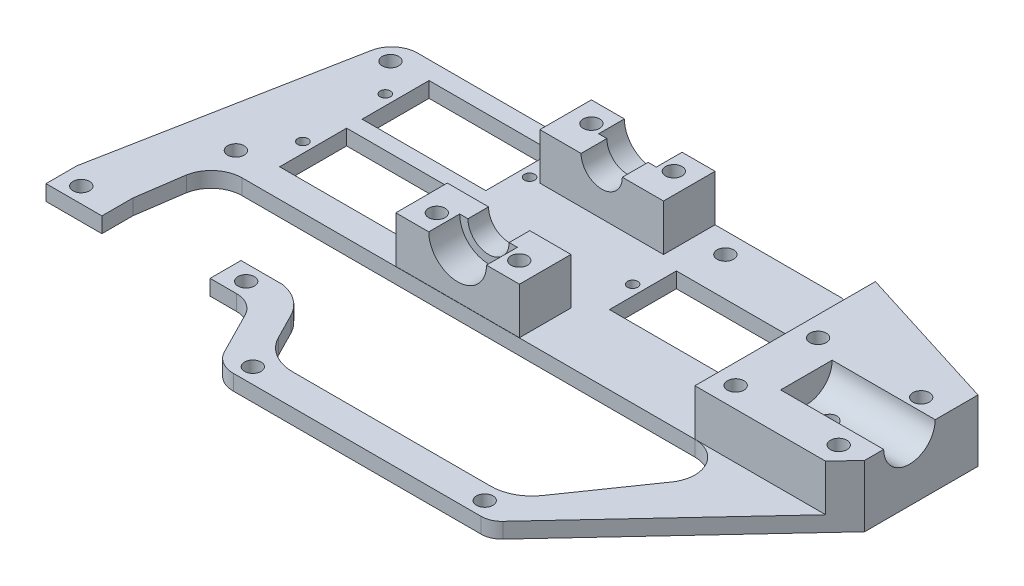
SolidWorks part; units mm, degrees
ref_plane "Спереди" through (0, 0, 0) normal (0, 0, 1) x (1, 0, 0)
ref_plane "Сверху" through (0, 0, 0) normal (0, 1, 0) x (1, 0, 0)
ref_plane "Справа" through (0, 0, 0) normal (1, 0, 0) x (0, 0, -1)
sketch "Эскиз1" plane through (0, 0, 0) normal (0, 1, 0) x (1, 0, 0)
  line L0 (0, 20) -> (0, -20) construction
  line L1 (16, 6.5) -> (40, 6.5)
  line L2 (-40, 14.5) -> (-16, 14.5)
  line L3 (-40, 14.5) -> (-40, 1.5)
  line L4 (-40, 1.5) -> (-16, 1.5)
  line L5 (-16, 14.5) -> (-16, 1.5)
  line L6 (-40, 14.5) -> (-16, 1.5) construction
  line L7 (-40, 1.5) -> (-16, 14.5) construction
  line L8 (-40, -1.5) -> (-16, -1.5)
  line L9 (-40, -1.5) -> (-40, -14.5)
  line L10 (-40, -14.5) -> (-16, -14.5)
  line L11 (-16, -1.5) -> (-16, -14.5)
  line L12 (-40, -1.5) -> (-16, -14.5) construction
  line L13 (-40, -14.5) -> (-16, -1.5) construction
  line L14 (-28, 8) -> (-28, -8) construction
  line L15 (0, 20) -> (-56.8521, 20) construction
  line L16 (0, 20) -> (59.9648, 20) construction
  line L17 (0, -20) -> (57.5525, -20) construction
  line L18 (0, -20) -> (-56.8521, -20) construction
  line L19 (16, 6.5) -> (16, -6.5)
  line L20 (16, -6.5) -> (40, -6.5)
  line L21 (40, 6.5) -> (40, -6.5)
  line L22 (16, 6.5) -> (40, -6.5) construction
  line L23 (16, -6.5) -> (40, 6.5) construction
  line L24 (28, 20) -> (28, -20) construction
  line L25 (-56.8521, 14) -> (93.1479, 14) construction
  line L26 (-56.8521, -16) -> (93.1479, -16) construction
  line L27 (-40, -37) -> (-56, -37) construction
  line L28 (-40, -37) -> (-24, -37) construction
  line L29 (-40, -14.5) -> (-40, -37) construction
  line L30 (-59.8465, -34) -> (-19.8465, -34) construction
  line L31 (-19.8465, -34) -> (-19.8465, -40) construction
  line L32 (-19.8465, -40) -> (-59.8465, -40) construction
  line L33 (-59.8465, -40) -> (-59.8465, -34) construction
  line L34 (-59.8465, -34) -> (-49.8878, 18)
  line L35 (36.6127, 18) -> (-49.8878, 18)
  line L36 (36.6127, 18) -> (75.1122, 5.9202)
  line L37 (-47.6771, -24.9007) -> (-49.0001, -34)
  line L38 (50, -16) -> (70, -16) construction
  line L39 (-59.8465, -34) -> (-59.8465, -40)
  line L40 (-59.8465, -40) -> (-19.8465, -40)
  line L41 (-19.8465, -40) -> (-14.2549, -50.9742)
  line L42 (-9.7998, -53.7042) -> (38.319, -53.7042)
  line L43 (75.1122, 5.9202) -> (75.1122, -16.0798)
  line L44 (50, 0) -> (50, -16) construction
  line L45 (-4.2859, -47.7018) -> (34.1658, -47.7018)
  line L46 (-49.0001, -34) -> (-22.2977, -34)
  line L47 (-13.9887, -38.2804) -> (-11.4139, -43.3337)
  line L48 (-41.7786, -20) -> (46.0945, -20)
  line L49 (40.7412, -44.2586) -> (51.0261, -29.4176)
  line L50 (-20.5914, -50.7042) -> (71.7063, -50.7042) construction
  line L51 (-20.5914, -53.7042) -> (73.7938, -53.7042) construction
  line L52 (0, -16) -> (0, -104.4432) construction
  line L53 (-47, 14) -> (-47, -16) construction
  line L54 (50, 0) -> (70, -16) construction
  line L55 (-44.6457, 8) -> (-11.6511, 8) construction
  line L56 (-47.6771, -8) -> (-3.6396, -8) construction
  line L57 (8, 0) -> (46.0945, 0) construction
  line L58 (50, 0) -> (70, 0) construction
  line L59 (75.1122, -16.0798) -> (41.2457, -52.4308)
  line L60 (-49.0001, -34) -> (-49.0001, -40) construction
  line L61 (-22.2977, -34) -> (-19.8465, -34)
  circle A0 centre (-8, 14) radius 1.6
  circle A1 centre (8, 14) radius 1.6
  circle A2 centre (-8, -16) radius 1.6
  circle A3 centre (8, -16) radius 1.6
  circle A4 centre (-47, 14) radius 1.6
  circle A5 centre (70, 0) radius 1.6
  circle A6 centre (50, 0) radius 1.6
  circle A7 centre (18, 14) radius 1.6
  circle A8 centre (-47, -16) radius 1.6
  circle A9 centre (-56, -37) radius 1.6
  circle A10 centre (-24, -37) radius 1.6
  circle A11 centre (50, -16) radius 1.6
  circle A12 centre (70, -16) radius 1.6
  arc A13 (-41.7786, -20) -> (-47.6771, -24.9007) centre (-41.7786, -26) ccw
  arc A14 (-19.8465, -34) -> (-13.9887, -38.2804) centre (-21.3286, -42.1767) cw
  arc A15 (-4.2859, -47.7018) -> (-11.4139, -43.3337) centre (-4.2859, -39.7018) cw
  arc A16 (40.7412, -44.2586) -> (34.1658, -47.7018) centre (34.1658, -39.7018) cw
  arc A17 (51.0261, -29.4176) -> (46.0945, -20) centre (46.0945, -26) ccw
  arc A18 (41.2457, -52.4308) -> (38.319, -53.7042) centre (38.319, -49.7042) cw
  arc A19 (-9.7998, -53.7042) -> (-14.2549, -50.9742) centre (-9.7998, -48.7042) cw
  circle A20 centre (-9, -50.7042) radius 1.6
  circle A21 centre (36, -50.7042) radius 1.6
  circle A22 centre (60, -8) radius 1.6
  circle A23 centre (-42, -8) radius 1
  circle A24 centre (-14, -8) radius 1
  circle A25 centre (-42, 8) radius 1
  circle A26 centre (-14, 8) radius 1
  circle A27 centre (14, 0) radius 1
  circle A28 centre (42, 0) radius 1
  point P2 (-28, 8)
  point P7 (0, 0)
  point P10 (28, 0)
  point P11 (-28, -8)
  point P35 (0, 14)
  point P41 (0, -16)
  point P77 (-46.7637, -20)
  point P86 (40.0593, -53.7042)
  point P92 (-49.0001, -34)
  dimension "D10" = 16
  dimension "D12" = 16
  dimension "D14" = 10
  dimension "D18" = 40
  dimension "D23" = 20
  dimension "D26" = 6
  dimension "D31" = 125
  dimension "D32" = 3
  dimension "D33" = 45
  dimension "D36" = 28
  dimension "D21" = 4
  dimension "D1" = 13
  dimension "D2" = 24
  dimension "D3" = 28
  dimension "D4" = 28
  dimension "D5" = 20
  dimension "D6" = 12
  dimension "D7" = 3
  dimension "D8" = 6
  dimension "D9" = 4
  dimension "D11" = 8
  dimension "D13" = 8
  dimension "D15" = 20
  dimension "D16" = 50
  dimension "D17" = 32
  dimension "D19" = 6
  dimension "D20" = 3
  dimension "D22" = 6.0024
  dimension "D24" = 14
  dimension "D25" = 36
  dimension "D27" = 6
  dimension "D29" = 14
  dimension "D30" = 22
  dimension "D34" = 40
  dimension "D35" = 47
  dimension "D37" = 28
  dimension "D38" = 28
  dimension "D39" = 14
  dimension "D40" = 14
  dimension "D41" = 14
  dimension "D42" = 16
  dimension "D43" = 2
extrude "Бобышка-Вытянуть1" add sketch "Эскиз1" along normal blind 3
sketch "Эскиз2" plane through (0, 3, 0) normal (0, 1, 0) x (1, 0, 0)
  line L0 (46.1017, 15.0227) -> (46.0945, -20)
  line L2 (75.1122, 5.9202) -> (36.6127, 18) construction
  line L4 (46.0945, -20) -> (71.46, -20)
  line L10 (0, 18) -> (0, -19.9611) construction
  line L11 (12, 8) -> (-12, 8)
  line L12 (12, 8) -> (12, 18)
  line L13 (12, 18) -> (-12, 18)
  line L14 (-12, 8) -> (-12, 18)
  line L15 (12, 8) -> (-12, 18) construction
  line L16 (12, 18) -> (-12, 8) construction
  line L17 (12, -19.9611) -> (-12, -19.9611)
  line L18 (12, -19.9611) -> (12, -9.9611)
  line L19 (12, -9.9611) -> (-12, -9.9611)
  line L20 (-12, -19.9611) -> (-12, -9.9611)
  line L21 (12, -19.9611) -> (-12, -9.9611) construction
  line L22 (12, -9.9611) -> (-12, -19.9611) construction
  line L24 (75.1122, -16.0798) -> (75.1122, 5.9202)
  line L25 (41.2457, -52.4308) -> (75.1122, -16.0798) construction
  line L26 (71.46, -20) -> (75.1122, -16.0798)
  line L27 (46.1017, 15.0227) -> (75.1122, 5.9202)
  line L28 (36.6127, 18) -> (-49.8878, 18) construction
  circle A0 centre (50, 0) radius 1.6
  circle A1 centre (70, 0) radius 1.6
  circle A2 centre (70, -16) radius 1.6
  circle A3 centre (50, -16) radius 1.6
  circle A4 centre (-8, 14) radius 1.6
  circle A5 centre (8, 14) radius 1.6
  circle A6 centre (-8, -16) radius 1.6
  circle A7 centre (8, -16) radius 1.6
  circle A12 centre (60, -8) radius 1.6
  point P26 (0, 13)
  point P35 (0, -14.9611)
  point P65 (0, 18)
  dimension "D2" = 24
extrude "Бобышка-Вытянуть2" add sketch "Эскиз2" along normal blind 9
sketch "Эскиз3" plane through (75.1122, 0, 0) normal (1, 0, 0) x (0, 0, -1)
  line L0 (-16.0798, 12) -> (5.9202, 12) construction
  line L1 (-12.3846, 7) -> (-2.3846, 7) construction
  line L2 (-12.3846, 7) -> (-12.3846, 17) construction
  line L3 (-12.3846, 17) -> (-2.3846, 17) construction
  line L4 (-2.3846, 7) -> (-2.3846, 17) construction
  line L6 (-12.3846, 17) -> (-2.3846, 7) construction
  line L8 (-2.3846, 17) -> (-12.3846, 7) construction
  circle A0 centre (-7.3846, 12) radius 5
  point P8 (-7.3846, 12)
  dimension "D1" = 10
extrude "Вырез-Вытянуть1" cut sketch "Эскиз3" against normal blind 20
sketch "Эскиз4" plane through (0, 0, -18) normal (0, 0, -1) x (-1, 0, 0)
  line L1 (-12, 12) -> (12, 12) construction
  circle A0 centre (0, 12) radius 4
extrude "Вырез-Вытянуть2" cut sketch "Эскиз4" against normal through all
sketch "Эскиз6" plane through (0, 0, -18) normal (0, 0, -1) x (-1, 0, 0)
  circle A0 centre (0, 12) radius 5.6
extrude "Вырез-Вытянуть3" cut sketch "Эскиз6" against normal blind 5
sketch "Эскиз7" plane through (0, 0, 19.9611) normal (0, 0, 1) x (1, 0, 0)
  circle A0 centre (0, 12) radius 5.6
extrude "Вырез-Вытянуть4" cut sketch "Эскиз7" against normal blind 6
fillet "Скругление5" radius 5 1 edges at (-49.8878, 1.5, -18)
fillet "Скругление6" radius 5 1 edges at (-19.8465, 1.5, 40)
sketch "Эскиз8" plane through (0, 3, 0) normal (0, 1, 0) x (1, 0, 0)
  line L0 (-49.0001, -34) -> (-49.0001, -40)
  line L1 (-59.8465, -40) -> (-22.9105, -40) construction
  line L2 (-49.0001, -40) -> (-28.0001, -40)
  line L3 (-28.0001, -40) -> (-28.0001, -34)
  line L4 (-49.0001, -34) -> (-19.8465, -34) construction
  line L5 (-28.0001, -34) -> (-49.0001, -34)
  dimension "D1" = 21
extrude "Вырез-Вытянуть5" cut sketch "Эскиз8" against normal through all
